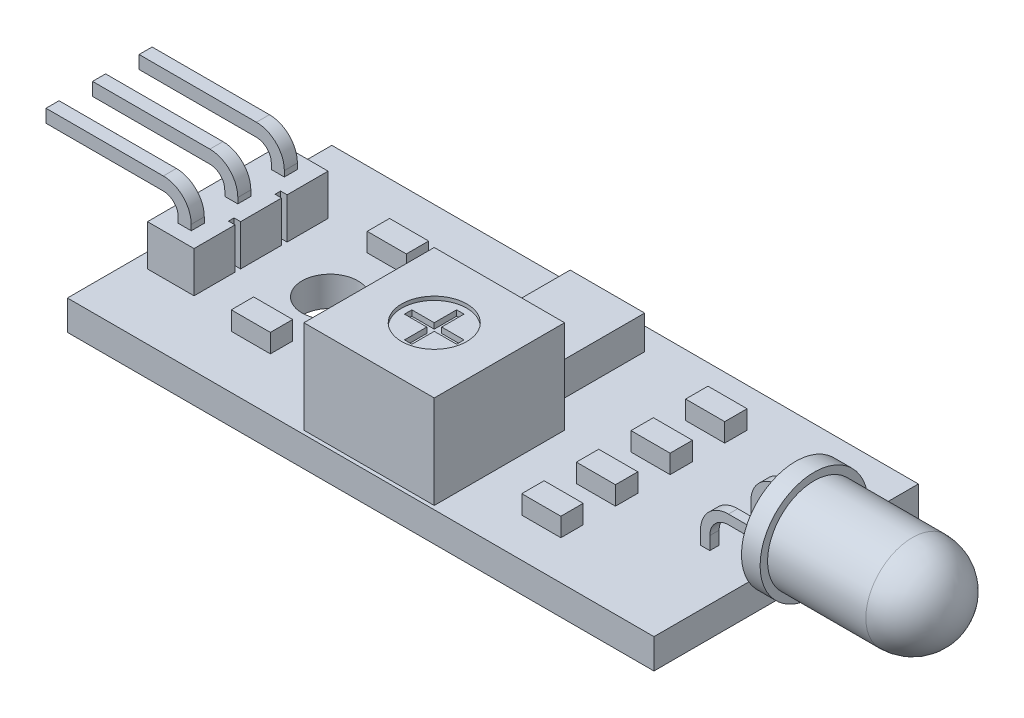
SolidWorks part; units mm, degrees
material "ABS"
ref_plane "Спереди" through (0, 0, 0) normal (0, 0, 1) x (1, 0, 0)
ref_plane "Сверху" through (0, 0, 0) normal (0, 1, 0) x (1, 0, 0)
ref_plane "Справа" through (0, 0, 0) normal (1, 0, 0) x (0, 0, -1)
sketch "Эскиз1" plane through (0, 0, 0) normal (0, 1, 0) x (1, 0, 0)
  line L0 (0, 0) -> (-18.3452, 0) construction
  line L1 (15.75, -7.1) -> (-15.75, -7.1)
  line L2 (15.75, -7.1) -> (15.75, 7.1)
  line L3 (15.75, 7.1) -> (-15.75, 7.1)
  line L4 (-15.75, -7.1) -> (-15.75, 7.1)
  line L5 (15.75, -7.1) -> (-15.75, 7.1) construction
  line L6 (15.75, 7.1) -> (-15.75, -7.1) construction
  circle A0 centre (-8.75, 0) radius 1.5
  point P0 (0, 0)
  dimension "D3" = 3
  dimension "D1" = 14.2
  dimension "D2" = 31.5
  dimension "D4" = 5.5
extrude "Бобышка-Вытянуть1" add sketch "Эскиз1" along normal blind 1.6
sketch "Эскиз2" plane through (0, 1.6, 0) normal (0, 1, 0) x (1, 0, 0)
  line L1 (-3.25, -6.9) -> (3.75, -6.9)
  line L2 (-3.25, -6.9) -> (-3.25, 0.1)
  line L3 (-3.25, 0.1) -> (3.75, 0.1)
  line L4 (3.75, -6.9) -> (3.75, 0.1)
  line L5 (-3.25, -6.9) -> (3.75, 0.1) construction
  line L6 (-3.25, 0.1) -> (3.75, -6.9) construction
  line L8 (-15.75, 7.1) -> (-15.75, -7.1) construction
  line L9 (-15.75, -7.1) -> (15.75, -7.1) construction
  point P0 (0.25, -3.4)
  dimension "D1" = 7
  dimension "D2" = 12.5
  dimension "D3" = 0.2
extrude "Бобышка-Вытянуть2" add sketch "Эскиз2" along normal blind 5
sketch "Эскиз3" plane through (0, 6.6, 0) normal (0, 1, 0) x (1, 0, 0)
  line L0 (-3.25, -3.4) -> (3.75, -3.4) construction
  line L1 (-3.25, 0.1) -> (-3.25, -6.9) construction
  line L2 (3.75, -6.9) -> (3.75, 0.1) construction
  line L3 (0.25, -3.4) -> (0.25, 5.936) construction
  circle A0 centre (0.25, -3.4) radius 1.75
  dimension "D1" = 3.5
extrude "Вырез-Вытянуть1" cut sketch "Эскиз3" against normal blind 0.2
sketch "Эскиз4" plane through (0, 6.4, 0) normal (0, 1, 0) x (1, 0, 0)
  line L0 (0.25, -3.4) -> (0.25, 6.0848) construction
  line L1 (0.25, -3.4) -> (3.05, -3.4) construction
  line L2 (0.05, -2) -> (0.45, -2)
  line L3 (0.45, -2) -> (0.45, -3.2)
  line L4 (0.45, -3.2) -> (1.65, -3.2)
  line L5 (1.65, -3.2) -> (1.65, -3.6)
  line L6 (0.45, -3.6) -> (1.65, -3.6)
  line L7 (0.45, -4.8) -> (0.45, -3.6)
  line L8 (0.05, -4.8) -> (0.45, -4.8)
  line L9 (0.05, -4.8) -> (0.05, -3.6)
  line L10 (0.05, -3.6) -> (-1.15, -3.6)
  line L11 (-1.15, -3.2) -> (-1.15, -3.6)
  line L12 (0.05, -3.2) -> (-1.15, -3.2)
  line L13 (0.05, -2) -> (0.05, -3.2)
  point P10 (1.65, -3.4)
  point P13 (-1.15, -3.4)
  point P15 (0.25, -4.8)
  point P20 (0.25, -2)
  dimension "D1" = 0.4
  dimension "D2" = 2.8
extrude "Вырез-Вытянуть2" cut sketch "Эскиз4" against normal blind 0.3
sketch "Эскиз6" plane through (0, 1.6, 0) normal (0, 1, 0) x (1, 0, 0)
  line L0 (15.75, 7.1) -> (-15.75, 7.1) construction
  line L1 (-1.75, 5.9) -> (2.25, 5.9)
  line L2 (-1.75, 5.9) -> (-1.75, 1.4)
  line L3 (-1.75, 1.4) -> (2.25, 1.4)
  line L4 (2.25, 5.9) -> (2.25, 1.4)
  line L5 (-15.75, 7.1) -> (-15.75, -7.1) construction
  dimension "D1" = 4
  dimension "D2" = 4.5
  dimension "D3" = 1.2
  dimension "D4" = 14
extrude "Бобышка-Вытянуть3" add sketch "Эскиз6" along normal blind 1.8
sketch "Эскиз7" plane through (0, 1.6, 0) normal (0, 1, 0) x (1, 0, 0)
  line L0 (-15.75, 0) -> (15.75, 0) construction
  line L1 (-15.75, 7.1) -> (-15.75, -7.1) construction
  line L2 (15.75, -7.1) -> (15.75, 7.1) construction
  line L3 (7.6, -5.2712) -> (7.6, 5.2712) construction
  line L4 (-8.75, -4.7808) -> (-8.75, 4.7808) construction
  line L5 (6.55, 2.0667) -> (8.65, 2.0667)
  line L6 (6.55, 2.0667) -> (6.55, 0.8667)
  line L7 (6.55, 0.8667) -> (8.65, 0.8667)
  line L8 (8.65, 2.0667) -> (8.65, 0.8667)
  line L9 (6.55, 2.0667) -> (8.65, 0.8667) construction
  line L10 (6.55, 0.8667) -> (8.65, 2.0667) construction
  line L11 (6.55, 5) -> (8.65, 5)
  line L12 (6.55, 5) -> (6.55, 3.8)
  line L13 (6.55, 3.8) -> (8.65, 3.8)
  line L14 (8.65, 5) -> (8.65, 3.8)
  line L15 (6.55, 5) -> (8.65, 3.8) construction
  line L16 (6.55, 3.8) -> (8.65, 5) construction
  line L17 (-5.75, -1.9) -> (-4.55, -4) construction
  line L18 (-9.8, 4.25) -> (-7.7, 4.25)
  line L19 (-9.8, 4.25) -> (-9.8, 3.05)
  line L20 (-9.8, 3.05) -> (-7.7, 3.05)
  line L21 (-7.7, 4.25) -> (-7.7, 3.05)
  line L22 (-9.8, 4.25) -> (-7.7, 3.05) construction
  line L23 (-9.8, 3.05) -> (-7.7, 4.25) construction
  line L24 (-5.75, 4) -> (-4.55, 4)
  line L25 (-5.75, 4) -> (-5.75, 1.9)
  line L26 (-5.75, 1.9) -> (-4.55, 1.9)
  line L27 (-4.55, 4) -> (-4.55, 1.9)
  line L28 (-5.75, 4) -> (-4.55, 1.9) construction
  line L29 (-5.75, 1.9) -> (-4.55, 4) construction
  line L30 (-5.75, -4) -> (-4.55, -1.9) construction
  line L31 (-9.8, -3.05) -> (-7.7, -4.25) construction
  line L32 (-9.8, -4.25) -> (-7.7, -3.05) construction
  line L33 (6.55, -3.8) -> (8.65, -5) construction
  line L34 (6.55, -5) -> (8.65, -3.8) construction
  line L35 (6.55, -0.8667) -> (8.65, -2.0667) construction
  line L36 (6.55, -2.0667) -> (8.65, -0.8667) construction
  line L37 (-4.55, -4) -> (-4.55, -1.9)
  line L38 (-5.75, -1.9) -> (-4.55, -1.9)
  line L39 (-5.75, -4) -> (-5.75, -1.9)
  line L40 (-5.75, -4) -> (-4.55, -4)
  line L41 (-7.7, -4.25) -> (-7.7, -3.05)
  line L42 (-9.8, -3.05) -> (-7.7, -3.05)
  line L43 (-9.8, -4.25) -> (-9.8, -3.05)
  line L44 (-9.8, -4.25) -> (-7.7, -4.25)
  line L45 (8.65, -5) -> (8.65, -3.8)
  line L46 (6.55, -3.8) -> (8.65, -3.8)
  line L47 (6.55, -5) -> (6.55, -3.8)
  line L48 (6.55, -5) -> (8.65, -5)
  line L49 (8.65, -2.0667) -> (8.65, -0.8667)
  line L50 (6.55, -0.8667) -> (8.65, -0.8667)
  line L51 (6.55, -2.0667) -> (6.55, -0.8667)
  line L52 (6.55, -2.0667) -> (8.65, -2.0667)
  line L53 (6.55, 3.8) -> (6.55, 2.0667) construction
  line L54 (6.55, 0.8667) -> (6.55, -0.8667) construction
  point P6 (-5.15, -2.95)
  point P8 (7.6, 1.4667)
  point P13 (7.6, 4.4)
  point P21 (-8.75, 3.65)
  point P26 (-5.15, 2.95)
  point P48 (-8.75, 0)
  point P49 (7.6, 0)
  point P50 (-8.75, -3.65)
  point P51 (7.6, -4.4)
  point P52 (7.6, -1.4667)
  dimension "D1" = 2.1
  dimension "D2" = 1.2
  dimension "D3" = 10
  dimension "D4" = 7.1
  dimension "D5" = 8
  dimension "D6" = 8.5
  dimension "D7" = 10
extrude "Бобышка-Вытянуть4" add sketch "Эскиз7" along normal blind 1
sketch "Эскиз9" plane through (0, 0, 0) normal (0, 0, 1) x (1, 0, 0)
  line L0 (12.75, 2.3) -> (12.75, -0.5)
  line L1 (12.75, -0.5) -> (13.25, -0.5)
  line L2 (13.25, -0.5) -> (13.25, 2.3)
  line L3 (14.25, 3.3) -> (16.25, 3.3)
  line L4 (16.25, 3.3) -> (16.25, 3.8)
  line L5 (16.25, 3.8) -> (14.25, 3.8)
  line L6 (-15.75, 0) -> (15.75, 0) construction
  line L7 (15.75, 1.6) -> (15.75, 0) construction
  line L8 (-15.75, 1.6) -> (15.75, 1.6) construction
  arc A0 (13.25, 2.3) -> (14.25, 3.3) centre (14.25, 2.3) cw
  arc A1 (12.75, 2.3) -> (14.25, 3.8) centre (14.25, 2.3) cw
  dimension "D6" = 1
  dimension "D7" = 1.5
  dimension "D1" = 0.5
  dimension "D2" = 0.5
  dimension "D3" = 2.5
  dimension "D4" = 2.2
  dimension "D5" = 0.5
extrude "Бобышка-Вытянуть5" add sketch "Эскиз9" against normal blind 0.5 from offset 1.6
pattern_linear "Линейный массив1" count 2 spacing 2.7 along (0, 0, -1) of "Бобышка-Вытянуть5"
sketch "Эскиз10" plane through (0, 0, 0) normal (0, 0, 1) x (1, 0, 0)
  line L0 (16.25, 3.55) -> (22.5604, 3.55) construction
  line L1 (16.25, 3.3) -> (16.25, 3.8) construction
  line L2 (16.25, 3.55) -> (16.25, 6.45)
  line L3 (16.25, 6.45) -> (17.25, 6.45)
  line L4 (17.25, 6.45) -> (17.25, 6.05)
  line L5 (17.25, 6.05) -> (22.53, 6.05)
  line L6 (16.25, 3.55) -> (25.03, 3.55)
  arc A0 (25.03, 3.55) -> (22.53, 6.05) centre (22.53, 3.55) ccw
  dimension "D1" = 5.8
  dimension "D2" = 5
  dimension "D3" = 1
  dimension "D4" = 8.78
revolve "Повернуть1" add sketch "Эскиз10" angle 360 about L0
sketch "Эскиз11" plane through (0, 0, 0) normal (0, 0, 1) x (1, 0, 0)
  line L0 (-13.35, -0.5) -> (-14.05, -0.5)
  line L1 (-14.05, -0.5) -> (-14.05, 4.1)
  line L2 (-14.85, 4.9) -> (-21.15, 4.9)
  line L3 (-21.15, 4.9) -> (-21.15, 5.6)
  line L4 (-21.15, 5.6) -> (-14.85, 5.6)
  line L5 (-13.35, 4.1) -> (-13.35, -0.5)
  line L6 (12.75, -0.5) -> (13.25, -0.5) construction
  line L7 (-15.75, 1.6) -> (-15.75, 0) construction
  line L8 (-15.75, 1.6) -> (15.75, 1.6) construction
  arc A0 (-14.85, 5.6) -> (-13.35, 4.1) centre (-14.85, 4.1) cw
  arc A1 (-14.05, 4.1) -> (-14.85, 4.9) centre (-14.85, 4.1) ccw
  dimension "D5" = 1.5
  dimension "D6" = 0.8
  dimension "D1" = 0.7
  dimension "D2" = 7.8
  dimension "D3" = 5.4
  dimension "D4" = 4
extrude "Бобышка-Вытянуть6" add sketch "Эскиз11" along normal mid plane 0.7
pattern_linear "Линейный массив2" count 2 spacing 2.5 along (0, 0, 1) of "Бобышка-Вытянуть6"
pattern_linear "Линейный массив3" count 2 spacing 2.5 along (0, 0, -1) of "Бобышка-Вытянуть6"
sketch "Эскиз12" plane through (0, 1.6, 0) normal (0, 1, 0) x (1, 0, 0)
  line L0 (-14.05, 0) -> (-13.35, 0) construction
  line L1 (-14.05, -0.35) -> (-14.05, 0.35) construction
  line L2 (-13.35, 0.35) -> (-13.35, -0.35) construction
  line L3 (-14.05, 2.5) -> (-13.35, 2.5) construction
  line L4 (-14.05, 2.15) -> (-14.05, 2.85) construction
  line L5 (-13.35, 2.85) -> (-13.35, 2.15) construction
  line L6 (-14.05, -2.5) -> (-13.35, -2.5) construction
  line L7 (-14.05, -2.85) -> (-14.05, -2.15) construction
  line L8 (-13.35, -2.15) -> (-13.35, -2.85) construction
  line L9 (-14.6, 1.4) -> (-14.6, 1.1)
  line L10 (-12.45, -1.4) -> (-14.95, -1.4)
  line L11 (-12.45, -1.4) -> (-12.45, -3.6)
  line L12 (-12.45, -3.6) -> (-14.95, -3.6)
  line L13 (-14.95, -1.4) -> (-14.95, -3.6)
  line L14 (-12.45, -1.4) -> (-14.95, -3.6) construction
  line L15 (-12.45, -3.6) -> (-14.95, -1.4) construction
  line L16 (-14.95, 1.1) -> (-12.45, 1.1)
  line L17 (-14.95, 1.1) -> (-14.95, -1.1)
  line L18 (-14.95, -1.1) -> (-12.45, -1.1)
  line L19 (-12.45, 1.1) -> (-12.45, -1.1)
  line L20 (-14.95, 1.1) -> (-12.45, -1.1) construction
  line L21 (-14.95, -1.1) -> (-12.45, 1.1) construction
  line L22 (-14.95, 3.6) -> (-12.45, 3.6)
  line L23 (-14.95, 3.6) -> (-14.95, 1.4)
  line L24 (-14.95, 1.4) -> (-12.45, 1.4)
  line L25 (-12.45, 3.6) -> (-12.45, 1.4)
  line L26 (-14.95, 3.6) -> (-12.45, 1.4) construction
  line L27 (-14.95, 1.4) -> (-12.45, 3.6) construction
  line L28 (-14.6, -1.1) -> (-14.6, -1.4)
  line L29 (-13.7, 0) -> (-13.7, 4.664) construction
  line L30 (-12.8, -1.1) -> (-12.8, -1.4)
  line L31 (-12.8, 1.4) -> (-12.8, 1.1)
  point P18 (-13.7, -2.5)
  point P23 (-13.7, 0)
  point P28 (-13.7, 2.5)
  dimension "D1" = 2.5
  dimension "D2" = 7.2
  dimension "D3" = 1.8
extrude "Бобышка-Вытянуть7" add sketch "Эскиз12" along normal blind 2.2 contours L25 L22 L23 L24 | L31 L24 L9 L16 | L19 L16 L17 L18 | L30 L18 L28 L10 | L10 L13 L12 L11
sketch "Эскиз13" plane through (0, 0, 0) normal (0, -1, 0) x (1, 0, 0)
  line L0 (0.25, -0.1) -> (0.25, 8.1547) construction
  line L1 (3.75, -0.1) -> (-3.25, -0.1) construction
  line L3 (-15.75, 7.1) -> (15.75, 7.1) construction
  circle A0 centre (-2.25, 3.6) radius 0.4
  circle A1 centre (0.25, 1.1) radius 0.4
  circle A2 centre (2.75, 3.6) radius 0.4
  dimension "D1" = 0.8
  dimension "D3" = 5
  dimension "D2" = 3.5
  dimension "D4" = 6
extrude "Бобышка-Вытянуть8" add sketch "Эскиз13" along normal up to surface (0.5 mm away) up to face at (13, -0.5, 1.35)
scale "Scale1" bodies to scale 116 scale about origin uniform scaling yes scale factor 0.04762
